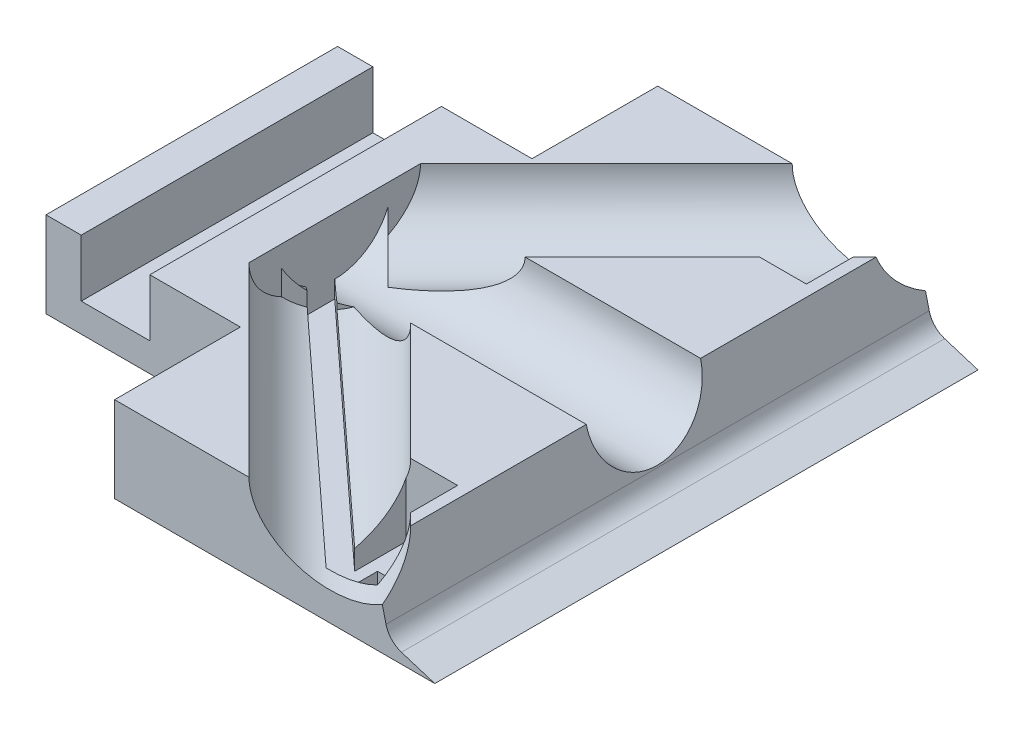
SolidWorks part; units mm, degrees
ref_plane "Front Plane" through (0, 0, 0) normal (0, 0, 1) x (1, 0, 0)
ref_plane "Top Plane" through (0, 0, 0) normal (0, 1, 0) x (1, 0, 0)
ref_plane "Right Plane" through (0, 0, 0) normal (1, 0, 0) x (0, 0, -1)
sketch "Sketch1" plane through (0, 0, 0) normal (0, 1, 0) x (1, 0, 0)
  line L1 (-45, -47.5) -> (45, -47.5)
  line L2 (-45, -47.5) -> (-45, 47.5)
  line L3 (-45, 47.5) -> (45, 47.5)
  line L4 (45, -47.5) -> (45, 47.5)
  line L5 (-45, -47.5) -> (45, 47.5) construction
  line L6 (-45, 47.5) -> (45, -47.5) construction
  point P0 (0, 0)
  dimension "D1" = 95
  dimension "D2" = 90
extrude "Boss-Extrude1" add sketch "Sketch1" along normal blind 20
sketch "Sketch2" plane through (45, 0, 0) normal (1, 0, 0) x (0, 0, -1)
  line L0 (-47.5, 0) -> (47.5, 0) construction
  line L1 (47.5, 20) -> (47.5, 0) construction
  circle A0 centre (0, 13) radius 10
  dimension "D1" = 13
  dimension "D2" = 47.5
extrude "Cut-Extrude2" cut sketch "Sketch2" against normal blind 70
sketch "Sketch3" plane through (0, 0, 47.5) normal (0, 0, 1) x (1, 0, 0)
  line L0 (45, 0) -> (37.4211, 1.8993)
  line L1 (37.4211, 1.8993) -> (30.2523, 20)
  line L2 (-45, 20) -> (45, 20) construction
  line L4 (30.2523, 20) -> (45, 20)
  line L7 (45, 20) -> (45, 0)
extrude "Cut-Extrude3" cut sketch "Sketch3" against normal blind 100
sketch "Sketch5" plane through (0, 0, 47.5) normal (0, 0, 1) x (1, 0, 0)
  line L0 (-45, 0) -> (45, 0) construction
  line L1 (-26.8384, 19) -> (-38.8384, 19)
  line L2 (-26.8384, 19) -> (-26.8384, 3)
  line L3 (-26.8384, 3) -> (-38.8384, 3)
  line L4 (-38.8384, 19) -> (-38.8384, 3)
  dimension "D1" = 12
  dimension "D2" = 3
  dimension "D3" = 16
extrude "Cut-Extrude5" cut sketch "Sketch5" against normal blind 100
fillet "Fillet2" radius 10 1 edges at (37.4211, 1.8993, 0)
sketch "Sketch6" plane through (0, 20, 0) normal (0, 1, 0) x (1, 0, 0)
  line L0 (30.2523, 47.5) -> (-45, 47.5) construction
  line L1 (-45, -47.5) -> (-21, -47.5)
  line L2 (-45, -47.5) -> (-45, 47.5)
  line L3 (-45, 47.5) -> (-21, 47.5)
  line L4 (-21, -47.5) -> (-21, 47.5)
  dimension "D1" = 24
extrude "Boss-Extrude2" add sketch "Sketch6" along normal blind 24
sketch "Sketch7" plane through (0, 20, 0) normal (0, 1, 0) x (1, 0, 0)
  line L0 (-21, -47.5) -> (30.2523, -47.5) construction
  line L1 (-19, -45.5) -> (28.2523, -45.5)
  line L2 (-19, -45.5) -> (-19, -11.5014)
  line L3 (-19, -11.5014) -> (28.2523, -11.5014)
  line L4 (28.2523, -45.5) -> (28.2523, -11.5014)
  line L5 (30.2523, -7.1414) -> (-21, -7.1414) construction
  line L6 (-21, -47.5) -> (-21, -7.1414) construction
  line L7 (30.2523, -7.1414) -> (30.2523, -47.5) construction
  dimension "D1" = 2
  dimension "D2" = 4.36
  dimension "D3" = 2
  dimension "D4" = 2
  dimension "D5" = 33.9986
extrude "Cut-Extrude7" cut sketch "Sketch7" against normal blind 17
sketch "Sketch8" plane through (0, 20, 0) normal (0, 1, 0) x (1, 0, 0)
  line L0 (30.2523, 47.5) -> (-21, 47.5) construction
  line L1 (-19, 11.5) -> (28.2523, 11.5)
  line L2 (-19, 11.5) -> (-19, 45.5)
  line L3 (-19, 45.5) -> (28.2523, 45.5)
  line L4 (28.2523, 11.5) -> (28.2523, 45.5)
  line L5 (30.2523, 47.5) -> (30.2523, 7.1414) construction
  line L6 (-21, 7.1414) -> (-21, 47.5) construction
  dimension "D1" = 2
  dimension "D2" = 34
  dimension "D3" = 2
  dimension "D4" = 2
extrude "Cut-Extrude8" cut sketch "Sketch8" against normal blind 17
sketch "Sketch10" plane through (-21, 0, 0) normal (1, 0, 0) x (0, 0, -1)
  line L1 (-47.5, 44) -> (47.5, 44)
  line L2 (-47.5, 44) -> (-47.5, 20)
  line L3 (-47.5, 20) -> (47.5, 20)
  line L4 (47.5, 44) -> (47.5, 20)
extrude "Boss-Extrude3" add sketch "Sketch10" along normal blind 25
sketch "Sketch12" plane through (-45, 0, 0) normal (-1, 0, 0) x (0, 0, 1)
  line L1 (47.5, 0) -> (25.5, 0)
  line L2 (47.5, 0) -> (47.5, 32)
  line L3 (47.5, 32) -> (25.5, 32)
  line L4 (25.5, 0) -> (25.5, 32)
  dimension "D1" = 32
  dimension "D2" = 22
extrude "Cut-Extrude9" cut sketch "Sketch12" against normal blind 34
sketch "Sketch13" plane through (-45, 0, 0) normal (-1, 0, 0) x (0, 0, 1)
  line L1 (-47.5, 0) -> (-25.5, 0)
  line L2 (-47.5, 0) -> (-47.5, 32)
  line L3 (-47.5, 32) -> (-25.5, 32)
  line L4 (-25.5, 0) -> (-25.5, 32)
  dimension "D1" = 22
  dimension "D2" = 32
extrude "Cut-Extrude10" cut sketch "Sketch13" against normal blind 34
sketch "Sketch14" plane through (0, 0, -47.5) normal (0, 0, -1) x (-1, 0, 0)
  line L0 (11, 32) -> (45, 32) construction
  circle A0 centre (31.5228, 44) radius 10
  dimension "D1" = 12
extrude "Cut-Extrude11" cut sketch "Sketch14" against normal blind 100
sketch "Sketch18" plane through (0, 0, -47.5) normal (0, 0, -1) x (-1, 0, 0)
  line L0 (11, 32) -> (45, 32) construction
  line L1 (-4, 44) -> (15.5228, 44)
  line L2 (-4, 44) -> (-4, 32)
  line L3 (-4, 32) -> (15.5228, 32)
  line L4 (15.5228, 44) -> (15.5228, 32)
  dimension "D1" = 6
extrude "Cut-Extrude13" cut sketch "Sketch18" against normal blind 100
sketch "Sketch19" plane through (-25, 0, 0) normal (1, 0, 0) x (0, 0, -1)
  circle A0 centre (0, 13) radius 10
  arc A1 (-7.1414, 20) -> (7.1414, 20) centre (0, 13) ccw construction
  dimension "D1" = 0
extrude "Boss-Extrude5" add sketch "Sketch19" along normal blind 60
sketch "Sketch20" plane through (0, 0, 47.5) normal (0, 0, 1) x (1, 0, 0)
  line L1 (30.2523, 20) -> (45, 20)
  line L2 (30.2523, 20) -> (30.2523, 0)
  line L3 (30.2523, 0) -> (45, 0)
  line L4 (45, 20) -> (45, 0)
extrude "Boss-Extrude6" add sketch "Sketch20" against normal blind 95
sketch "Sketch21" plane through (0, 20, 0) normal (0, 1, 0) x (1, 0, 0)
  line L1 (45, -47.5) -> (4, -47.5)
  line L2 (45, -47.5) -> (45, 47.5)
  line L3 (45, 47.5) -> (4, 47.5)
  line L4 (4, -47.5) -> (4, 47.5)
extrude "Cut-Extrude16" cut sketch "Sketch21" along normal blind 17
sketch "Sketch23" plane through (0, 0, 47.5) normal (0, 0, 1) x (1, 0, 0)
  line L1 (-11, 32) -> (4, 32)
  line L2 (-11, 32) -> (-11, 20)
  line L3 (-11, 20) -> (4, 20)
  line L4 (4, 32) -> (4, 20)
extrude "Cut-Extrude17" cut sketch "Sketch23" against normal blind 100
sketch "Sketch29" plane through (0, 0, 47.5) normal (0, 0, 1) x (1, 0, 0)
  line L1 (-45, 32) -> (-3.6177, 32)
  line L2 (-45, 32) -> (-45, 73.2631)
  line L3 (-45, 73.2631) -> (-3.6177, 73.2631)
  line L4 (-3.6177, 32) -> (-3.6177, 73.2631)
extrude "Cut-Extrude22" cut sketch "Sketch29" against normal blind 100
sketch "Sketch30" plane through (0, 0, 25.5) normal (0, 0, 1) x (1, 0, 0)
  line L1 (-11, 32) -> (-19, 32)
  line L2 (-11, 32) -> (-11, 20)
  line L3 (-11, 20) -> (-19, 20)
  line L4 (-19, 32) -> (-19, 20)
extrude "Cut-Extrude23" cut sketch "Sketch30" against normal blind 100
sketch "Sketch31" plane through (0, 20, 0) normal (0, 1, 0) x (1, 0, 0)
  line L1 (-19, -11.5014) -> (28.2523, -11.5014)
  line L2 (-19, -11.5014) -> (-19, 11.5)
  line L3 (-19, 11.5) -> (28.2523, 11.5)
  line L4 (28.2523, -11.5014) -> (28.2523, 11.5)
extrude "Cut-Extrude24" cut sketch "Sketch31" against normal blind 17
sketch "Sketch33" plane through (0, 3, 0) normal (0, 1, 0) x (1, 0, 0)
  line L1 (-11, -45.5) -> (28.2523, -45.5)
  line L2 (-11, -45.5) -> (-11, 45.5)
  line L3 (-11, 45.5) -> (28.2523, 45.5)
  line L4 (28.2523, -45.5) -> (28.2523, 45.5)
extrude "Boss-Extrude7" add sketch "Sketch33" along normal blind 17
sketch "Sketch34" plane through (0, 3, 0) normal (0, 1, 0) x (1, 0, 0)
  line L0 (-19, -25.5) -> (-11, -25.5) construction
  line L1 (-11, 25.5) -> (-19, 25.5)
  line L2 (-11, 25.5) -> (-11, -25.5)
  line L3 (-11, -25.5) -> (-19, -25.5)
  line L4 (-19, 25.5) -> (-19, -25.5)
extrude "Boss-Extrude8" add sketch "Sketch34" along normal blind 17
sketch "Sketch35" plane through (0, 20, 0) normal (0, 1, 0) x (1, 0, 0)
  line L0 (45, -64.5) -> (62, -47.5)
  line L1 (45, -47.5) -> (62, -47.5)
  line L2 (45, -47.5) -> (45, -64.5)
  dimension "D1" = 17
  dimension "D2" = 17
extrude "Boss-Extrude10" add sketch "Sketch35" against normal blind 20 separate body
sketch "Sketch36" plane through (0, 20, 0) normal (0, 1, 0) x (1, 0, 0)
  line L0 (62, 47.5) -> (45, 64.5)
  line L1 (45, 47.5) -> (62, 47.5)
  line L2 (45, 47.5) -> (45, 64.5)
  dimension "D1" = 17
  dimension "D2" = 17
extrude "Boss-Extrude13" add sketch "Sketch36" against normal blind 20 separate body contours L0 L2 L1
sketch "Sketch43" plane through (54.75, 0, 54.75) normal (0.7071, 0, 0.7071) x (0.7071, 0, -0.7071)
  line L0 (-13.7886, 0) -> (10.253, 0) construction
  line L1 (10.253, 0) -> (10.253, 20) construction
  circle A0 centre (-14.747, 13) radius 10
  dimension "D1" = 13
  dimension "D2" = 25
extrude "Cut-Extrude35" cut sketch "Sketch43" against normal blind 85
sketch "Sketch44" plane through (54.75, 0, -54.75) normal (0.7071, 0, -0.7071) x (-0.7071, 0, -0.7071)
  line L0 (-10.253, 0) -> (13.7886, 0) construction
  line L1 (-10.253, 0) -> (-10.253, 20) construction
  circle A0 centre (14.747, 13) radius 10
  dimension "D1" = 13
  dimension "D2" = 25
extrude "Cut-Extrude36" cut sketch "Sketch44" against normal blind 85
sketch "Sketch45" plane through (0, 20, 0) normal (0, 1, 0) x (1, 0, 0)
  line L1 (45, -47.5) -> (70.4011, -47.5)
  line L2 (45, -47.5) -> (45, -70.3456)
  line L3 (45, -70.3456) -> (70.4011, -70.3456)
  line L4 (70.4011, -47.5) -> (70.4011, -70.3456)
extrude "Cut-Extrude37" cut sketch "Sketch45" against normal blind 85
sketch "Sketch46" plane through (0, 20, 0) normal (0, 1, 0) x (1, 0, 0)
  line L1 (45, 47.5) -> (66.6361, 47.5)
  line L2 (45, 47.5) -> (45, 69.6416)
  line L3 (45, 69.6416) -> (66.6361, 69.6416)
  line L4 (66.6361, 47.5) -> (66.6361, 69.6416)
extrude "Cut-Extrude38" cut sketch "Sketch46" against normal blind 85
sketch "Sketch48" plane through (45, 0, 0) normal (1, 0, 0) x (0, 0, -1)
  line L0 (-47.5, 0) -> (47.5, 0) construction
  line L1 (47.5, 0) -> (47.5, 20) construction
  circle A0 centre (0, 13) radius 10
  dimension "D1" = 13
  dimension "D2" = 47.5
extrude "Cut-Extrude40" cut sketch "Sketch48" against normal blind 65
sketch "Sketch49" plane through (0, 0, -47.5) normal (0, 0, -1) x (-1, 0, 0)
  circle A0 centre (-68.1577, 31.3858) radius 38.8043
extrude "Cut-Extrude41" cut sketch "Sketch49" against normal blind 100
sketch "Sketch50" plane through (0, 0, 0) normal (0, -1, 0) x (-1, 0, 0)
  line L0 (11, -47.5) -> (-45, -47.5) construction
  line L1 (-38, -45.5) -> (-28, -45.5)
  line L2 (-38, -45.5) -> (-38, -28.5)
  line L3 (-38, -28.5) -> (-28, -28.5)
  line L4 (-28, -45.5) -> (-28, -28.5)
  line L5 (-45, -47.5) -> (-45, 47.5) construction
  dimension "D1" = 17
  dimension "D2" = 10
  dimension "D3" = 2
  dimension "D4" = 7
extrude "Cut-Extrude43" cut sketch "Sketch50" against normal blind 4
sketch "Sketch51" plane through (0, 0, 0) normal (0, -1, 0) x (-1, 0, 0)
  line L0 (-45, -47.5) -> (-45, 47.5) construction
  line L1 (-38, 28.5) -> (-28, 28.5)
  line L2 (-38, 28.5) -> (-38, 45.5)
  line L3 (-38, 45.5) -> (-28, 45.5)
  line L4 (-28, 28.5) -> (-28, 45.5)
  line L5 (-45, 47.5) -> (11, 47.5) construction
  dimension "D1" = 17
  dimension "D2" = 10
  dimension "D3" = 7
  dimension "D4" = 2
extrude "Cut-Extrude44" cut sketch "Sketch51" against normal blind 4
sketch "Sketch52" plane through (0, 20, 0) normal (0, 1, 0) x (1, 0, 0)
  line L0 (31.0614, -7.1414) -> (-3.6144, -7.1414) construction
  line L1 (31.0614, -41.8172) -> (31.0614, -7.1414) construction
  circle A0 centre (26.0614, -27.1414) radius 3
  dimension "D1" = 20
  dimension "D2" = 5
extrude "Cut-Extrude45" cut sketch "Sketch52" against normal blind 100
sketch "Sketch53" plane through (0, 20, 0) normal (0, 1, 0) x (1, 0, 0)
  line L0 (-3.6144, 7.1414) -> (31.0614, 7.1414) construction
  line L1 (31.0614, 7.1414) -> (31.0614, 41.8172) construction
  circle A0 centre (26.0614, 27.1414) radius 3
  dimension "D1" = 20
  dimension "D2" = 5
extrude "Cut-Extrude46" cut sketch "Sketch53" against normal blind 100
sketch "Sketch54" plane through (-20, 0, 0) normal (1, 0, 0) x (0, 0, -1)
  line L1 (-10, 13) -> (66.5355, 13)
  line L3 (-10, 31.15) -> (66.5355, 31.15)
  line L4 (66.5355, 13) -> (66.5355, 31.15)
  line L5 (-10, 13) -> (-56.0211, 13)
  line L7 (-10, 31.15) -> (-56.0211, 31.15)
  line L8 (-56.0211, 13) -> (-56.0211, 31.15)
  arc A0 (-7.1414, 20) -> (7.1414, 20) centre (0, 13) ccw construction
extrude "Cut-Extrude47" cut sketch "Sketch54" along normal blind 300
sketch "Sketch55" plane through (0, 0, 25.5) normal (0, 0, 1) x (1, 0, 0)
  line L1 (-38.8384, 19) -> (-69.436, 19)
  line L3 (-38.8384, 41.9777) -> (-69.436, 41.9777)
  line L4 (-69.436, 19) -> (-69.436, 41.9777)
  line L5 (-38.8384, 19) -> (-7.7562, 19)
  line L6 (-38.8384, 41.9777) -> (-38.8384, 52.6636)
  line L7 (-38.8384, 52.6636) -> (-7.7562, 52.6636)
  line L8 (-7.7562, 19) -> (-7.7562, 52.6636)
extrude "Cut-Extrude48" cut sketch "Sketch55" against normal blind 300
sketch "Sketch57" plane through (0, 4, 0) normal (0, -1, 0) x (-1, 0, 0)
  line L1 (-38, -45.5) -> (-28, -45.5)
  line L2 (-38, -45.5) -> (-38, -28.5)
  line L3 (-38, -28.5) -> (-28, -28.5)
  line L4 (-28, -45.5) -> (-28, -28.5)
  line L5 (-38, 28.5) -> (-28, 28.5)
  line L6 (-38, 28.5) -> (-38, 45.5)
  line L7 (-38, 45.5) -> (-28, 45.5)
  line L8 (-28, 28.5) -> (-28, 45.5)
  dimension "D1" = 10
  dimension "D2" = 17
  dimension "D3" = 17
extrude "Boss-Extrude15" add sketch "Sketch57" along normal blind 4
sketch "Sketch58" plane through (0, 0, 0) normal (0, -1, 0) x (-1, 0, 0)
  line L0 (11, 25.5) -> (11, 47.5)
  line L1 (45, 25.5) -> (11, 25.5)
  line L2 (45, 25.5) -> (45, -25.5)
  line L3 (45, -25.5) -> (11, -25.5)
  line L5 (11, -47.5) -> (-45, -47.5)
  line L6 (11, -47.5) -> (11, -25.5)
  line L7 (11, 47.5) -> (-45, 47.5)
  line L8 (-45, -47.5) -> (-45, 47.5)
extrude "Boss-Extrude16" add sketch "Sketch58" along normal blind 4
sketch "Sketch60" plane through (0, -4, 0) normal (0, -1, 0) x (-1, 0, 0)
  line L0 (11, -25.5) -> (11, -47.5)
  line L1 (-45, 47.5) -> (11, 47.5)
  line L2 (-45, 47.5) -> (-45, -47.5)
  line L3 (-45, -47.5) -> (11, -47.5)
  line L4 (11, 47.5) -> (11, 25.5)
  line L5 (45, -25.5) -> (11, -25.5)
  line L6 (45, -25.5) -> (45, 25.5)
  line L7 (45, 25.5) -> (11, 25.5)
extrude "Cut-Extrude49" cut sketch "Sketch60" against normal blind 2
sketch "Sketch61" plane through (0, 0, -47.5) normal (0, 0, -1) x (-1, 0, 0)
  line L0 (-45, -2) -> (-37, 0.5)
  line L1 (-37, 0.5) -> (-33.9855, 13)
  line L2 (-33.9855, 13) -> (-46.9602, 4.2727)
  line L3 (-46.9602, 4.2727) -> (-45, -2)
  line L4 (11, -2) -> (-45, -2) construction
  dimension "D1" = 2.5
  dimension "D2" = 8
extrude "Cut-Extrude51" cut sketch "Sketch61" against normal blind 100
fillet "Fillet3" radius 4 1 edges at (37, 0.5, 0)
sketch "Sketch63" plane through (-5.3541, 0, 5.3541) normal (0.7071, 0, -0.7071) x (-0.7071, 0, -0.7071)
  circle A0 centre (14.747, 13) radius 10
extrude "Cut-Extrude52" cut sketch "Sketch63" along normal blind 65
sketch "Sketch65" plane through (-5.3541, 0, -5.3541) normal (0.7071, 0, 0.7071) x (0.7071, 0, -0.7071)
  circle A0 centre (-14.747, 13) radius 10
extrude "Cut-Extrude53" cut sketch "Sketch65" along normal blind 65
sketch "Sketch66" plane through (0, 0, -25.5) normal (0, 0, -1) x (-1, 0, 0)
  line L1 (20, 13) -> (45, 13)
  line L2 (20, 13) -> (20, 19)
  line L3 (20, 19) -> (45, 19)
  line L4 (45, 13) -> (45, 19)
extrude "Cut-Extrude54" cut sketch "Sketch66" against normal blind 65
sketch "Sketch68" plane through (0, 13, 0) normal (0, 1, 0) x (1, 0, 0)
  line L1 (-26.8384, 25.5) -> (-20, 25.5)
  line L2 (-26.8384, 25.5) -> (-26.8384, -9.2918)
  line L4 (-20, 25.5) -> (-20, -9.2918)
  line L6 (-20, -9.2918) -> (-20, -25.5)
  line L7 (-20, -25.5) -> (-26.8384, -25.5)
  line L8 (-26.8384, -9.2918) -> (-26.8384, -25.5)
extrude "Boss-Extrude17" add sketch "Sketch68" against normal blind 15
sketch "Sketch70" plane through (0, 13, 0) normal (0, 1, 0) x (1, 0, 0)
  circle A0 centre (26.0614, 27.1414) radius 3
extrude "Boss-Extrude18" add sketch "Sketch70" against normal blind 15
sketch "Sketch72" plane through (0, 13, 0) normal (0, 1, 0) x (1, 0, 0)
  line L0 (33.9855, 10) -> (33.9855, 40.6987) construction
  line L1 (22.9855, 44.5) -> (31.9855, 44.5)
  line L2 (22.9855, 44.5) -> (22.9855, 30.5)
  line L3 (22.9855, 30.5) -> (31.9855, 30.5)
  line L4 (31.9855, 44.5) -> (31.9855, 30.5)
  dimension "D1" = 2
  dimension "D2" = 3
  dimension "D3" = 14
  dimension "D4" = 9
extrude "Cut-Extrude56" cut sketch "Sketch72" against normal blind 12
sketch "Sketch73" plane through (0, 0, 0) normal (0, 1, 0) x (1, 0, 0)
  circle A0 centre (26.0614, -27.1414) radius 3
extrude "Boss-Extrude20" add sketch "Sketch73" along normal blind 13
sketch "Sketch74" plane through (0, 13, 0) normal (0, 1, 0) x (1, 0, 0)
  line L1 (22.9855, -30.5) -> (31.9855, -30.5)
  line L2 (22.9855, -30.5) -> (22.9855, -44.5)
  line L3 (22.9855, -44.5) -> (31.9855, -44.5)
  line L4 (31.9855, -30.5) -> (31.9855, -44.5)
  dimension "D1" = 14
  dimension "D2" = 9
  dimension "D3" = 2
  dimension "D4" = 3
extrude "Cut-Extrude57" cut sketch "Sketch74" against normal blind 13
sketch "Sketch75" plane through (0, 0, 0) normal (0, 1, 0) x (1, 0, 0)
  line L0 (22.9855, -30.5) -> (22.9855, -44.5) construction
  line L1 (24.9855, -42.5) -> (29.9855, -42.5)
  line L2 (24.9855, -42.5) -> (24.9855, -37.5)
  line L3 (24.9855, -37.5) -> (29.9855, -37.5)
  line L4 (29.9855, -42.5) -> (29.9855, -37.5)
  line L5 (31.9855, -44.5) -> (31.9855, -30.5) construction
  line L6 (22.9855, -44.5) -> (31.9855, -44.5) construction
  line L7 (22.9855, 44.5) -> (31.9855, 44.5) construction
  line L8 (29.9855, 37.5) -> (24.9855, 37.5)
  line L9 (29.9855, 37.5) -> (29.9855, 42.5)
  line L10 (29.9855, 42.5) -> (24.9855, 42.5)
  line L11 (24.9855, 37.5) -> (24.9855, 42.5)
  dimension "D1" = 2
  dimension "D2" = 2
  dimension "D3" = 2
  dimension "D4" = 5
  dimension "D5" = 5
  dimension "D6" = 2
extrude "Cut-Extrude58" cut sketch "Sketch75" against normal blind 13
sketch "Sketch76" plane through (0, 0, 0) normal (0, -1, 0) x (-1, 0, 0)
  line L0 (-24.9855, 42.5) -> (-24.9855, 37.5) construction
  line L1 (-29.9855, 37.5) -> (-24.9855, 37.5)
  line L2 (-29.9855, 37.5) -> (-29.9855, 42.5)
  line L3 (-29.9855, 42.5) -> (-24.9855, 42.5)
  line L4 (-24.9855, 37.5) -> (-24.9855, 42.5)
extrude "Cut-Extrude59" cut sketch "Sketch76" against normal blind 13
sketch "Sketch77" plane through (0, 13, 0) normal (0, 1, 0) x (1, 0, 0)
  line L0 (22.9855, -39.5) -> (-20, 0)
  line L1 (22.9855, -30.5) -> (22.9855, -44.5) construction
  line L2 (-20, -9.2918) -> (-20, 9.2918) construction
  line L3 (22.9855, -39.5) -> (22.9855, -44.5)
  line L4 (22.9855, -44.5) -> (-20, -5)
  line L5 (-20, -14.9975) -> (-20, 14.9975) construction
  line L6 (-20, -5) -> (-20, 0)
  dimension "D2" = 5
  dimension "D3" = 5
extrude "Cut-Extrude63" cut sketch "Sketch77" against normal blind 13
sketch "Sketch84" plane through (0, 1, 0) normal (0, 1, 0) x (1, 0, 0)
  line L1 (22.9855, 44.5) -> (31.9855, 44.5)
  line L2 (22.9855, 44.5) -> (22.9855, 30.5)
  line L3 (22.9855, 30.5) -> (31.9855, 30.5)
  line L4 (31.9855, 44.5) -> (31.9855, 30.5)
  line L5 (29.9855, 37.5) -> (24.9855, 37.5)
  line L6 (29.9855, 37.5) -> (29.9855, 42.5)
  line L7 (29.9855, 42.5) -> (24.9855, 42.5)
  line L8 (24.9855, 37.5) -> (24.9855, 42.5)
extrude "Cut-Extrude71" cut sketch "Sketch84" against normal blind 1
